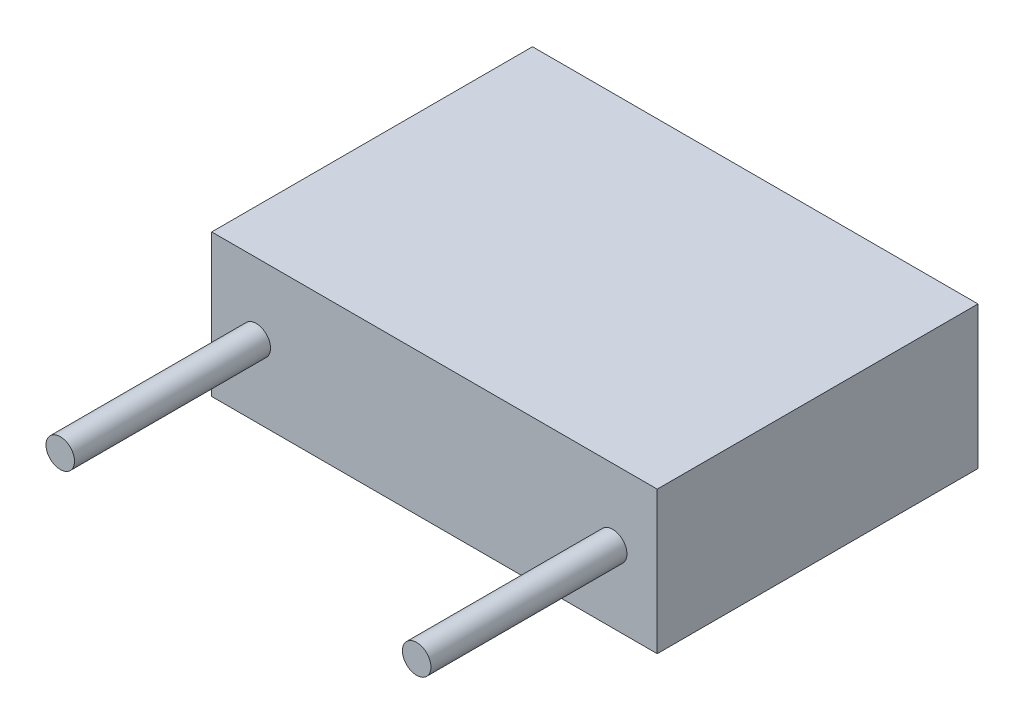
SolidWorks part; units mm, degrees
ref_plane "Спереди" through (0, 0, 0) normal (0, 0, 1) x (1, 0, 0)
ref_plane "Сверху" through (0, 0, 0) normal (0, 1, 0) x (1, 0, 0)
ref_plane "Справа" through (0, 0, 0) normal (1, 0, 0) x (0, 0, -1)
sketch "Эскиз1" plane through (0, 0, 0) normal (0, 0, 1) x (1, 0, 0)
  line L1 (0, 0) -> (12.5, 0)
  line L2 (0, 0) -> (0, 4)
  line L3 (0, 4) -> (12.5, 4)
  line L4 (12.5, 0) -> (12.5, 4)
  dimension "D1" = 12.5
  dimension "D2" = 4
extrude "Бобышка-Вытянуть1" add sketch "Эскиз1" along normal blind 9
sketch "Эскиз2" plane through (0, 0, 9) normal (0, 0, 1) x (1, 0, 0)
  line L0 (0, 4) -> (0, 0) construction
  line L1 (12.5, 4) -> (0, 4) construction
  circle A0 centre (1.25, 2) radius 0.4
  circle A1 centre (11.25, 2) radius 0.4
  dimension "D1" = 0.8
  dimension "D2" = 10
  dimension "D3" = 1.25
  dimension "D4" = 2
extrude "Бобышка-Вытянуть2" add sketch "Эскиз2" along normal blind 5.5
